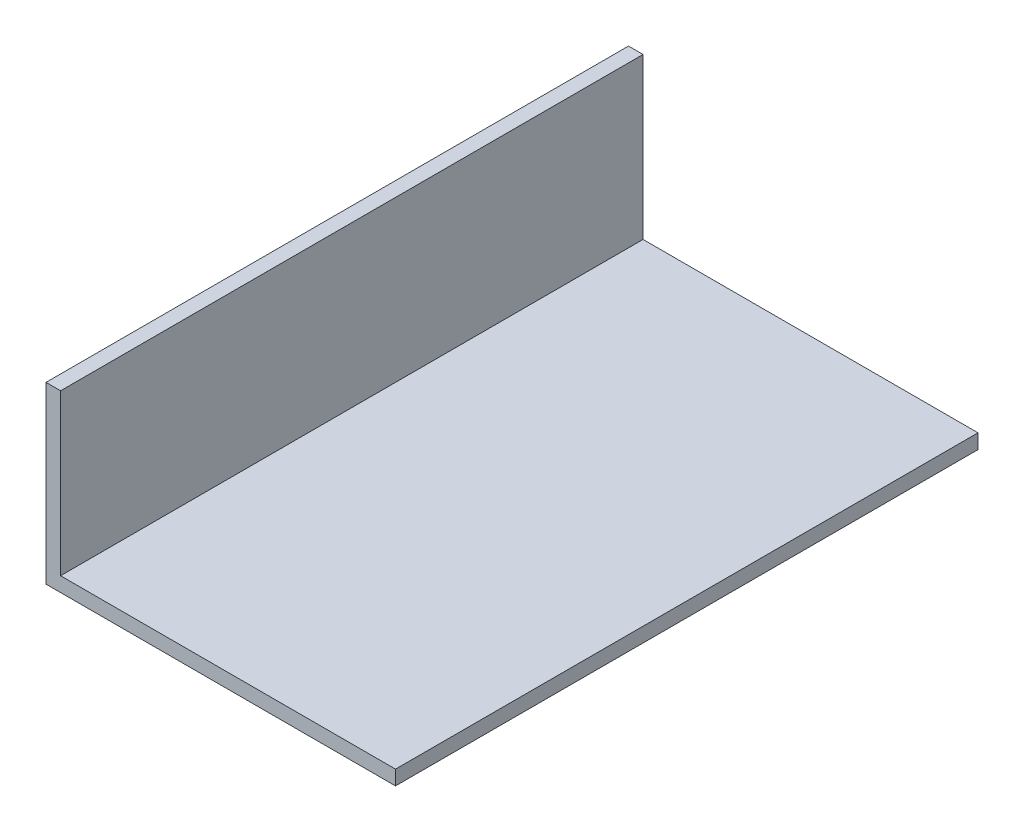
SolidWorks part; units mm, degrees
material "1060 Alloy"
ref_plane "Front Plane" through (0, 0, 0) normal (0, 0, 1) x (1, 0, 0)
ref_plane "Top Plane" through (0, 0, 0) normal (0, 1, 0) x (1, 0, 0)
ref_plane "Right Plane" through (0, 0, 0) normal (1, 0, 0) x (0, 0, -1)
sketch "Sketch1" plane through (0, 0, 0) normal (0, 0, 1) x (1, 0, 0)
  line L0 (0, 0) -> (76.2, 0)
  line L1 (76.2, 0) -> (76.2, 3.175)
  line L2 (76.2, 3.175) -> (3.175, 3.175)
  line L3 (3.175, 3.175) -> (3.175, 38.1)
  line L4 (3.175, 38.1) -> (0, 38.1)
  line L5 (0, 38.1) -> (0, 0)
  dimension "D1" = 3.175
  dimension "D2" = 76.2
  dimension "D3" = 38.1
extrude "Boss-Extrude1" add sketch "Sketch1" along normal blind 127
